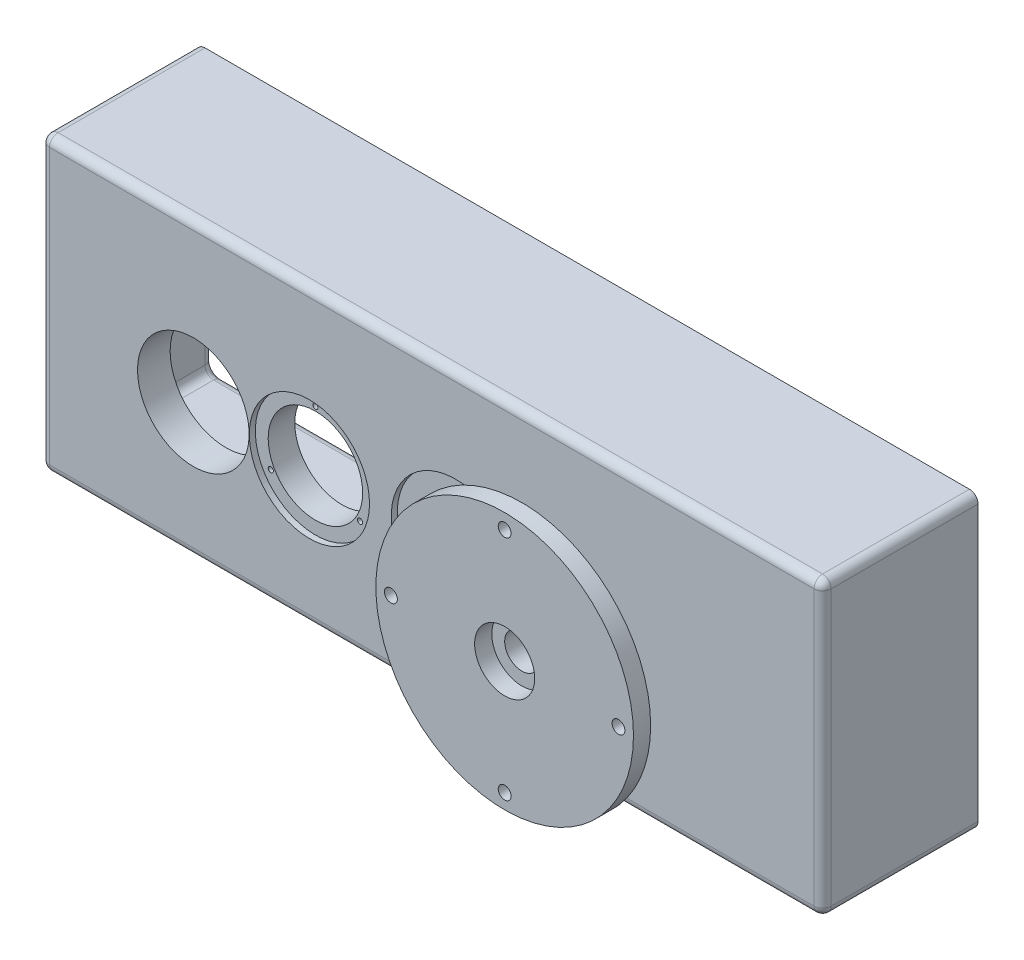
SolidWorks part; units mm, degrees
ref_plane "Front Plane" through (0, 0, 0) normal (0, 0, 1) x (1, 0, 0)
ref_plane "Top Plane" through (0, 0, 0) normal (0, 1, 0) x (1, 0, 0)
ref_plane "Right Plane" through (0, 0, 0) normal (1, 0, 0) x (0, 0, -1)
sketch "Sketch1" plane through (0, 0, 0) normal (0, 0, 1) x (1, 0, 0)
  line L0 (-87.4128, 56.4012) -> (822.7771, 56.4012)
  line L1 (822.7771, 56.4012) -> (822.7771, -283.5988)
  line L2 (-87.4128, 56.4012) -> (-87.4128, -283.5988)
  line L3 (-87.4128, -283.5988) -> (822.7771, -283.5988)
extrude "Boss-Extrude1" add sketch "Sketch1" along normal blind 38
sketch "Sketch2" plane through (0, 0, 0) normal (0, 0, -1) x (-1, 0, 0)
  line L0 (87.4128, 56.4012) -> (87.4128, -126.6388)
  line L1 (87.4128, 56.4012) -> (87.4128, -283.5988) construction
  line L2 (87.4128, -126.6388) -> (-90.0272, -126.6388)
  line L3 (-90.0272, -126.6388) -> (-225.1972, -126.6388)
  line L4 (-225.1972, -126.6388) -> (-395.51, -126.6388)
  line L5 (-395.51, -126.6388) -> (-532.59, -126.6388)
  circle A0 centre (-90.0272, -126.6388) radius 65
  circle A1 centre (-225.1972, -126.6388) radius 55
  circle A2 centre (-395.51, -126.6388) radius 45
  circle A3 centre (-532.59, -126.6388) radius 20
  dimension "D1" = 183.04
  dimension "D2" = 177.44
extrude "Cut-Extrude1" cut sketch "Sketch2" against normal through all
sketch "Sketch4" plane through (0, 0, 0) normal (0, 0, -1) x (-1, 0, 0)
  circle A0 centre (-532.59, -126.6388) radius 30
  circle A1 centre (-395.51, -126.6388) radius 55
  circle A2 centre (-225.1972, -126.6388) radius 65
  circle A3 centre (-90.0272, -126.6388) radius 70
extrude "Cut-Extrude2" cut sketch "Sketch4" against normal blind 11 flip side to cut
sketch "Sketch6" plane through (0, 0, 11) normal (0, 0, -1) x (-1, 0, 0)
  line L0 (-822.7771, 56.4012) -> (87.4128, 56.4012)
  line L1 (87.4128, 56.4012) -> (87.4128, -283.5988)
  line L2 (87.4128, -283.5988) -> (-822.7771, -283.5988)
  line L3 (-822.7771, -283.5988) -> (-822.7771, 56.4012)
  line L4 (-822.7771, 56.4012) -> (-802.7771, 56.4012)
  line L5 (-822.7771, -283.5988) -> (-822.7771, -263.5988)
  line L6 (-802.7771, 38.5938) -> (-802.7771, -263.5988)
  line L7 (87.4128, -283.5988) -> (87.4128, -263.5988)
  line L8 (87.4128, 56.4012) -> (67.4128, 56.4012)
  line L9 (-802.7771, -263.5988) -> (67.4128, -263.5988)
  line L10 (87.4128, 56.4012) -> (87.4128, 36.4012)
  line L11 (67.4128, -263.5988) -> (67.4128, 36.4012)
  line L12 (67.4128, 36.4012) -> (-802.7771, 36.4012)
sketch "Sketch10" plane through (0, 0, 11) normal (0, 0, -1) x (-1, 0, 0)
  line L1 (-822.7771, 56.4012) -> (87.4128, 56.4012)
  line L2 (-822.7771, 56.4012) -> (-822.7771, -283.5988)
  line L3 (-822.7771, -283.5988) -> (87.4128, -283.5988)
  line L4 (87.4128, 56.4012) -> (87.4128, -283.5988)
  line L5 (-802.7771, 38.5938) -> (67.4128, 38.5938)
  line L6 (-802.7771, 38.5938) -> (-802.7771, -263.5988)
  line L7 (-802.7771, -263.5988) -> (67.4128, -263.5988)
  line L8 (67.4128, 38.5938) -> (67.4128, -263.5988)
extrude "Boss-Extrude2" add sketch "Sketch10" along normal blind 154
fillet "Fillet1" radius 10 8 edges at (822.7771, 56.4012, -52.5) (822.7771, -283.5988, -52.5) (-87.4128, -283.5988, -52.5) (-87.4128, 56.4012, -52.5) (822.7771, -113.5988, 38) (367.6821, -283.5988, 38) (-87.4128, -113.5988, 38) (367.6821, 56.4012, 38)
sketch "Sketch11" plane through (0, 0, 38) normal (0, 0, 1) x (1, 0, 0)
  circle A0 centre (532.59, -126.6388) radius 35
  circle A1 centre (395.51, -126.6388) radius 75
  circle A2 centre (225.1972, -126.6388) radius 70
extrude "Cut-Extrude3" cut sketch "Sketch11" against normal blind 7
fillet "Fillet2" radius 10 12 edges at (802.7771, -112.5025, -143) (367.6821, 38.5938, -143) (367.6821, -263.5988, -143) (-67.4128, 38.5938, -66) (-67.4128, -112.5025, -143) (-67.4128, -263.5988, -66) (-67.4128, -112.5025, 11) (802.7771, -263.5988, -66) (802.7771, 38.5938, -66) (802.7771, -112.5025, 11) (367.6821, -263.5988, 11) (367.6821, 38.5938, 11)
sketch "Sketch12" plane through (0, 0, 38) normal (0, 0, 1) x (1, 0, 0)
  circle A0 centre (395.51, -126.6388) radius 60
  circle A1 centre (225.1972, -126.6388) radius 60
  circle A2 centre (225.1972, -66.6388) radius 3
  circle A3 centre (277.1587, -156.6388) radius 3
  circle A4 centre (173.2357, -156.6388) radius 3
  circle A5 centre (395.51, -66.6388) radius 3
  circle A6 centre (447.4715, -156.6388) radius 3
  circle A7 centre (343.5484, -156.6388) radius 3
  point P15 (225.1972, -126.6388)
  point P21 (395.51, -126.6388)
  dimension "D1" = 3
  dimension "D2" = 3
extrude "Cut-Extrude4" cut sketch "Sketch12" against normal through all contours A2 | A4 | A3 | A5 | A7 | A6
sketch "Sketch15" plane through (0, 0, 38) normal (0, 0, 1) x (1, 0, 0)
  circle A0 centre (532.59, -126.6388) radius 20
  circle A1 centre (532.59, -126.6388) radius 35
extrude "Boss-Extrude3" add sketch "Sketch15" along normal blind 60 separate body
sketch "Sketch20" plane through (0, 0, 98) normal (0, 0, 1) x (1, 0, 0)
  circle A0 centre (532.59, -126.6388) radius 35
  circle A1 centre (532.59, -126.6388) radius 150
extrude "Boss-Extrude4" add sketch "Sketch20" along normal blind 20 separate body
sketch "Sketch21" plane through (0, 0, 118) normal (0, 0, 1) x (1, 0, 0)
  circle A0 centre (532.59, -126.6388) radius 132.5
  circle A1 centre (532.59, 5.8612) radius 7.5
  circle A2 centre (665.09, -126.6388) radius 7.5
  circle A3 centre (532.59, -259.1388) radius 7.5
  circle A4 centre (400.09, -126.6388) radius 7.5
  point P14 (532.59, -126.6388)
  dimension "D1" = 265
  dimension "D2" = 4
extrude "Cut-Extrude7" cut sketch "Sketch21" against normal blind 46 contours A1 | A2 | A4 | A3
